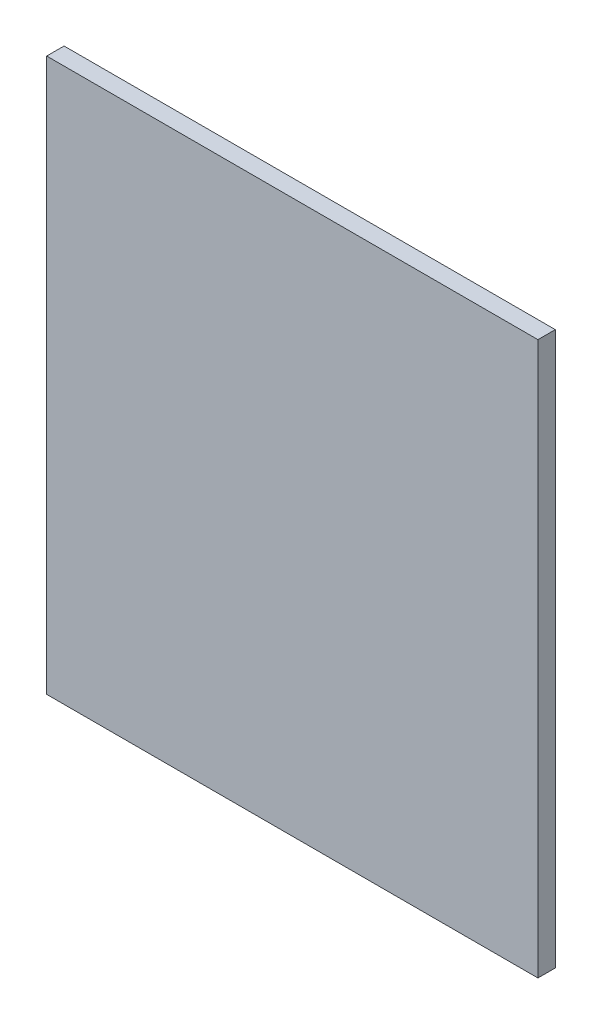
SolidWorks part; units mm, degrees
ref_plane "Front Plane" through (0, 0, 0) normal (0, 0, 1) x (1, 0, 0)
ref_plane "Top Plane" through (0, 0, 0) normal (0, 1, 0) x (1, 0, 0)
ref_plane "Right Plane" through (0, 0, 0) normal (1, 0, 0) x (0, 0, -1)
sketch "Sketch1" plane through (0, 0, 0) normal (0, 1, 0) x (1, 0, 0)
  line L13 (0, 0) -> (78.994, 0)
  line L14 (0, 0) -> (0, 2.794)
  line L15 (0, 2.794) -> (78.994, 2.794)
  line L16 (78.994, 0) -> (78.994, 2.794)
  dimension "D1" = 78.994
  dimension "D2" = 2.794
extrude "Boss-Extrude1" add sketch "Sketch1" along normal blind 88.9
